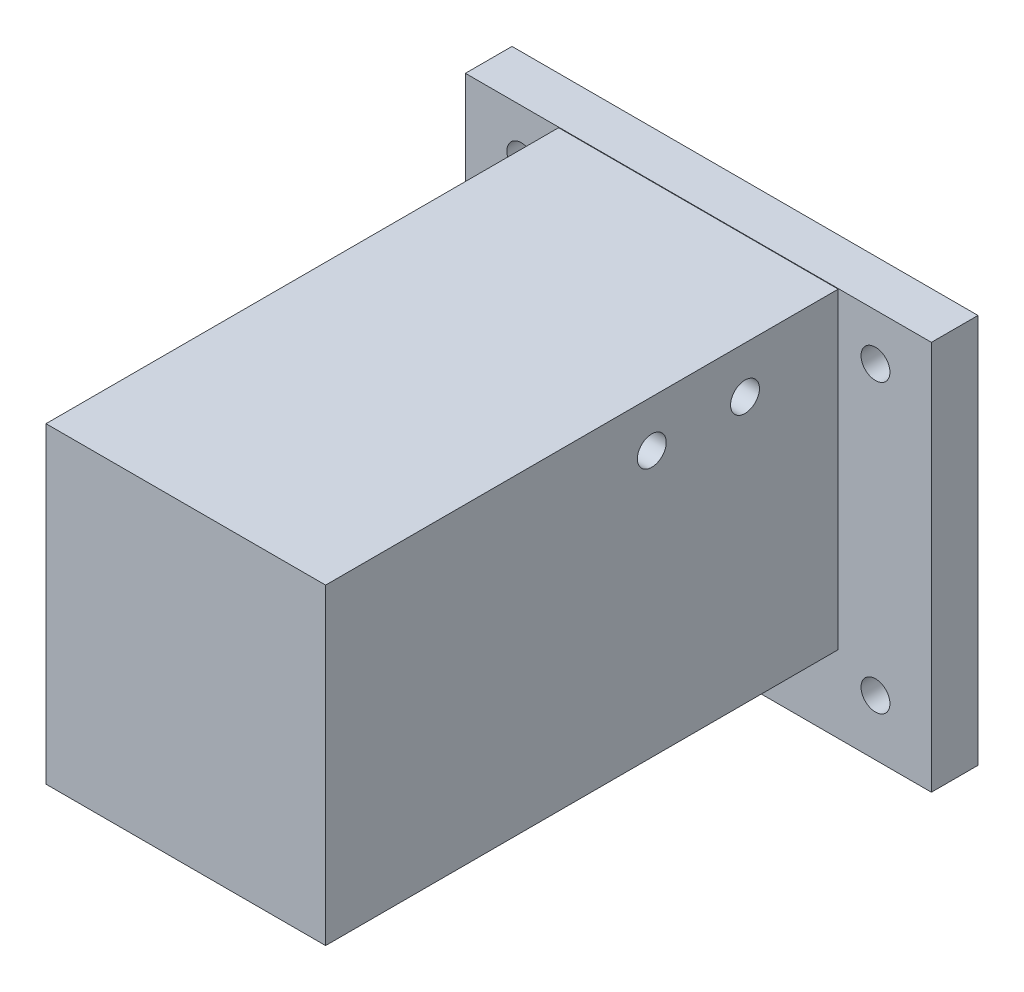
SolidWorks part; units mm, degrees
ref_plane "Front Plane" through (0, 0, 0) normal (0, 0, 1) x (1, 0, 0)
ref_plane "Top Plane" through (0, 0, 0) normal (0, 1, 0) x (1, 0, 0)
ref_plane "Right Plane" through (0, 0, 0) normal (1, 0, 0) x (0, 0, -1)
sketch "Sketch3" plane through (0, 0, 0) normal (0, 0, 1) x (1, 0, 0)
  line L1 (-25, 25) -> (25, 25)
  line L2 (-25, 25) -> (-25, -25)
  line L3 (-25, -25) -> (25, -25)
  line L4 (25, 25) -> (25, -25)
  line L5 (-25, 25) -> (25, -25) construction
  line L6 (-25, -25) -> (25, 25) construction
  point P0 (0, 0)
  dimension "D1" = 50
  dimension "D2" = 50
extrude "Boss-Extrude1" add sketch "Sketch3" along normal blind 5
sketch "Sketch4" plane through (0, 0, 0) normal (0, 0, 1) x (1, 0, 0)
  line L1 (-15, 16.75) -> (15, 16.75)
  line L2 (-15, 16.75) -> (-15, -16.75)
  line L3 (-15, -16.75) -> (15, -16.75)
  line L4 (15, 16.75) -> (15, -16.75)
  line L5 (-15, 16.75) -> (15, -16.75) construction
  line L6 (-15, -16.75) -> (15, 16.75) construction
  point P0 (0, 0)
  dimension "D1" = 30
  dimension "D2" = 33.5
extrude "Boss-Extrude4" add sketch "Sketch4" along normal blind 70 from offset 5
sketch "Sketch6" plane through (0, 0, 0) normal (0, 1, 0) x (1, 0, 0)
  line L0 (0, 0) -> (0, -77.5486) construction
  line L1 (15, -75) -> (15, -5) construction
  line L2 (-10, -15) -> (10, -15)
  line L3 (-10, -15) -> (-10, -56)
  line L4 (-10, -56) -> (10, -56)
  line L5 (10, -15) -> (10, -56)
  line L6 (-15, -75) -> (-15, -5) construction
  dimension "D1" = 5
  dimension "D2" = 5
  dimension "D3" = 15
  dimension "D4" = 41
extrude "Cut-Extrude1" cut sketch "Sketch6" against normal blind 19 from offset 2 contours L3 L2 L5 L4
sketch "Sketch7" plane through (0, 0, 0) normal (0, 1, 0) x (1, 0, 0)
  line L0 (15, -75) -> (15, -5) construction
  line L1 (-15, -75) -> (15, -75)
  line L2 (-15, -75) -> (-15, -60)
  line L3 (-15, -60) -> (15, -60)
  line L4 (15, -75) -> (15, -60)
  line L6 (-15, -60) -> (10, -60)
  line L7 (-15, -60) -> (-15, -56)
  line L8 (-15, -56) -> (10, -56)
  line L9 (10, -60) -> (10, -56)
  dimension "D1" = 4
extrude "Cut-Extrude2" cut sketch "Sketch7" against normal through all both and the other way through all contours L1 L4 L3 L2
sketch "Sketch9" plane through (0, 0, 0) normal (1, 0, 0) x (0, 0, -1)
  line L0 (-60, 16.75) -> (-5, 16.75) construction
  line L3 (-5, 16.75) -> (-5, -16.75) construction
  circle A0 centre (-25, 11.75) radius 1.55
  circle A1 centre (-15, 11.75) radius 1.55
  point P9 (-25, 16.75)
  dimension "D1" = 3.1
  dimension "D2" = 5
  dimension "D3" = 10
  dimension "D4" = 10
extrude "Cut-Extrude4" cut sketch "Sketch9" against normal through all both and the other way through all contours A0 | A1
sketch "Sketch10" plane through (0, 0, 0) normal (0, 0, 1) x (1, 0, 0)
  line L0 (-49.8652, 0) -> (49.8652, 0) construction
  line L1 (0, -27.967) -> (0, 27.967) construction
  line L2 (0, 0) -> (-25, 25)
  line L3 (0, 0) -> (25, 25)
  line L4 (-25, 25) -> (-25, -25) construction
  circle A0 centre (-19, 19) radius 1.55
  circle A1 centre (19, 19) radius 1.55
  circle A2 centre (19, -19) radius 1.55
  circle A3 centre (-19, -19) radius 1.55
  point P4 (0, 0)
  point P8 (0, 0)
  point P23 (-19, 19)
  point P24 (0, 0)
  dimension "D1" = 3.1
  dimension "D2" = 6
extrude "Cut-Extrude6" cut sketch "Sketch10" against normal through all and the other way through all contours L2 A0 | A3 | A2 | A1
sketch "Sketch11" plane through (0, 0, 5) normal (0, 0, 1) x (1, 0, 0)
  line L0 (25, -25) -> (25, 25) construction
  line L1 (-25, 25) -> (25, 25)
  line L2 (-25, 25) -> (-25, 16.8069)
  line L3 (-25, 16.8069) -> (25, 16.8069)
  line L4 (25, 25) -> (25, 16.8069)
extrude "Cut-Extrude7" cut sketch "Sketch11" against normal blind 25
sketch "Sketch12" plane through (0, 0, 0) normal (0, 0, 1) x (1, 0, 0)
  line L0 (-19, -68.3766) -> (-19, 29.6201) construction
  line L1 (-25, 16.8069) -> (25, 16.8069) construction
  line L2 (0, -29.6201) -> (0, 29.6201) construction
  circle A0 centre (-19, 11.8069) radius 1.55
  circle A1 centre (19, 11.8069) radius 1.55
  point P4 (-19, -19.3783)
  point P12 (0, 0)
  dimension "D1" = 3.1
  dimension "D2" = 5
extrude "Cut-Extrude8" cut sketch "Sketch12" against normal blind 25 and the other way through all contours A0 | A1
